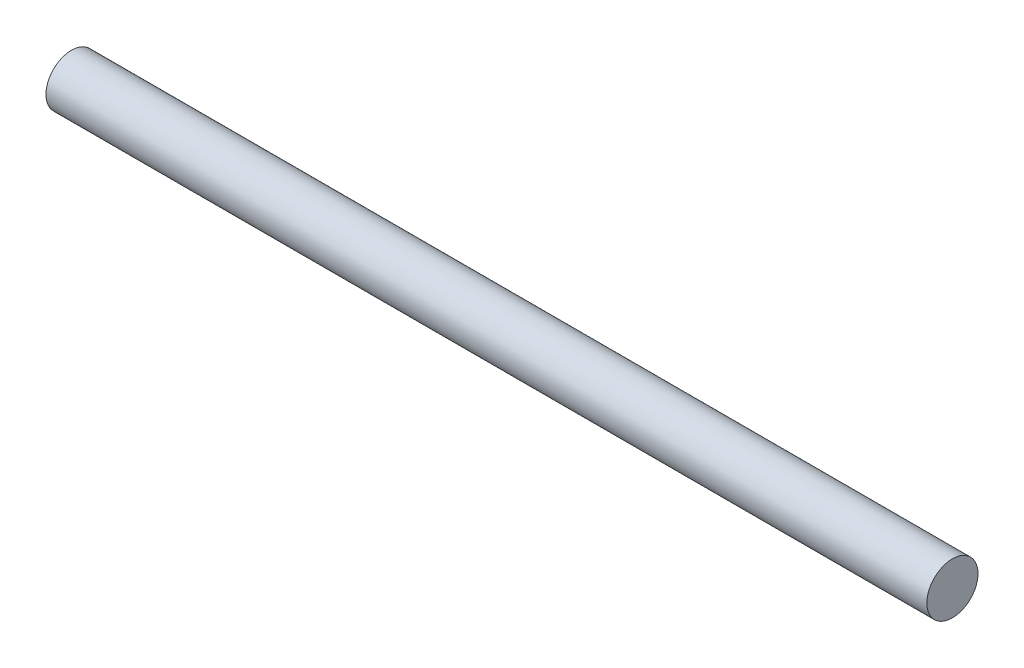
SolidWorks part; units mm, degrees
ref_plane "Plan de face" through (0, 0, 0) normal (0, 0, 1) x (1, 0, 0)
ref_plane "Plan de dessus" through (0, 0, 0) normal (0, 1, 0) x (1, 0, 0)
ref_plane "Plan de droite" through (0, 0, 0) normal (1, 0, 0) x (0, 0, -1)
sketch "Esquisse5" plane through (0, 0, 0) normal (1, 0, 0) x (0, 0, -1)
  circle A0 centre (0, 0) radius 18
extrude "Boss.-Extru.3" add sketch "Esquisse5" along normal blind 620
ref_plane "Plan2" through (10, 0, 0) normal (-1, 0, 0) x (0, 0, 1)
ref_plane "Plan4" through (610, 0, 0) normal (-1, 0, 0) x (0, 0, 1)
sketch "Esquisse6" plane through (10, 0, 0) normal (-1, 0, 0) x (0, 0, 1)
  circle A0 centre (0, 0) radius 18
sketch "Esquisse7" plane through (610, 0, 0) normal (-1, 0, 0) x (0, 0, 1)
  circle A0 centre (0, 0) radius 18
ref_plane "Plan31" through (310, 0, 0) normal (-1, 0, 0) x (0, 0, 1)
sketch "Esquisse32" plane through (310, 0, 0) normal (-1, 0, 0) x (0, 0, 1)
  circle A0 centre (0, 0) radius 18
